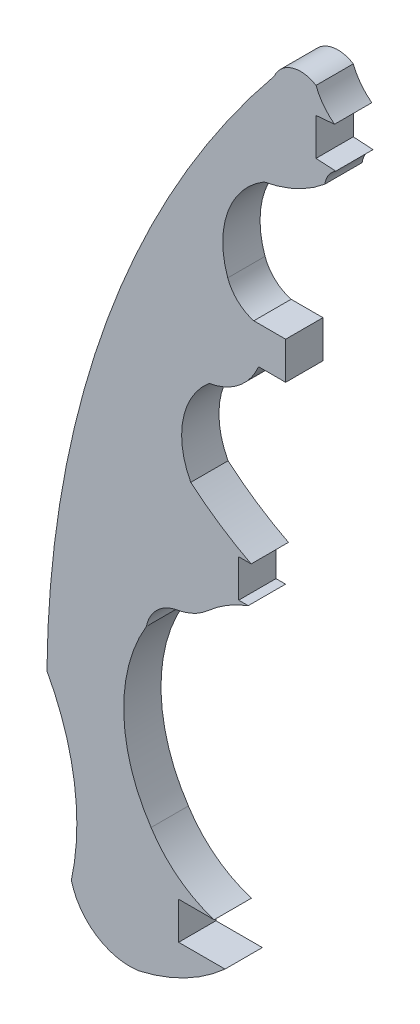
SolidWorks part; units mm, degrees
ref_plane "Front Plane" through (0, 0, 0) normal (0, 0, 1) x (1, 0, 0)
ref_plane "Top Plane" through (0, 0, 0) normal (0, 1, 0) x (1, 0, 0)
ref_plane "Right Plane" through (0, 0, 0) normal (1, 0, 0) x (0, 0, -1)
sketch "Sketch1" plane through (0, 0, 0) normal (0, 0, 1) x (1, 0, 0)
  line L0 (-110.8244, 0) -> (-110.8244, -1.524)
  line L1 (-110.8244, -1.524) -> (-108.9277, -1.524)
  line L2 (-110.8244, 0) -> (-109.3734, 0)
  line L3 (-104.4543, 30.6115) -> (-105.2112, 30.5448)
  line L4 (-105.2112, 30.5448) -> (-105.2112, 29.0254)
  line L5 (-105.2112, 29.0254) -> (-104.404, 28.9774)
  line L6 (-108.3692, 13.3481) -> (-108.3692, 11.8112)
  line L7 (-108.3692, 13.3481) -> (-107.8612, 13.3481)
  line L8 (-108.3692, 11.8112) -> (-107.9797, 11.8112)
  line L9 (-106.451, 22.0064) -> (-106.451, 20.4787)
  line L10 (-106.451, 20.4787) -> (-107.5577, 20.4787)
  line L11 (-106.451, 22.0064) -> (-107.7525, 22.0064)
  arc A0 (-108.9277, -1.524) -> (-112.4429, -3.3463) centre (-114.1894, 4.3239) cw
  arc A1 (-112.4429, -3.3463) -> (-115.2078, -1.524) centre (-112.8214, -0.9119) cw
  arc A2 (-116.2053, 5.3875) -> (-106.9169, 31.0817) centre (-74.9979, 5.0169) cw
  arc A3 (-115.2078, -1.524) -> (-116.2053, 5.3875) centre (-125.036, 0.5852) ccw
  arc A4 (-109.3734, 0) -> (-111.9502, 1.9761) centre (-107.9797, 4.4855) cw
  arc A5 (-106.9169, 31.0817) -> (-105.2112, 31.6087) centre (-105.8373, 30.6115) cw
  arc A6 (-105.2112, 31.6087) -> (-104.4543, 30.6115) centre (-103.0594, 32.4561) ccw
  arc A7 (-104.404, 28.9774) -> (-104.8497, 28.2927) centre (-103.8691, 28.1419) ccw
  arc A8 (-104.8497, 28.2927) -> (-107.334, 27.1314) centre (-108.2807, 32.3945) cw
  arc A10 (-109.6282, 10.811) -> (-110.8909, 10.205) centre (-111.3159, 12.7092) cw
  arc A11 (-110.8909, 10.205) -> (-112.1439, 8.9941) centre (-110.6329, 8.6843) ccw
  arc A12 (-112.1439, 8.9941) -> (-111.9502, 1.9761) centre (-106.52, 5.6376) ccw
  arc A13 (-107.9797, 11.8112) -> (-109.6282, 10.811) centre (-106.0775, 6.8174) ccw
  arc A14 (-107.7525, 22.0064) -> (-108.8173, 22.9927) centre (-107.3339, 23.5263) cw
  arc A15 (-108.8173, 22.9927) -> (-107.334, 27.1314) centre (-105.5655, 24.1624) cw
  arc A16 (-107.5577, 20.4787) -> (-109.5792, 18.8788) centre (-110.028, 21.5229) cw
  arc A17 (-109.5792, 18.8788) -> (-110.3289, 15.0014) centre (-107.5807, 16.4812) ccw
  arc A18 (-107.8612, 13.3481) -> (-110.3289, 15.0014) centre (-101.9181, 24.8868) cw
  dimension "D1" = 2.54
extrude "Boss-Extrude1" add sketch "Sketch1" along normal blind 1.524
